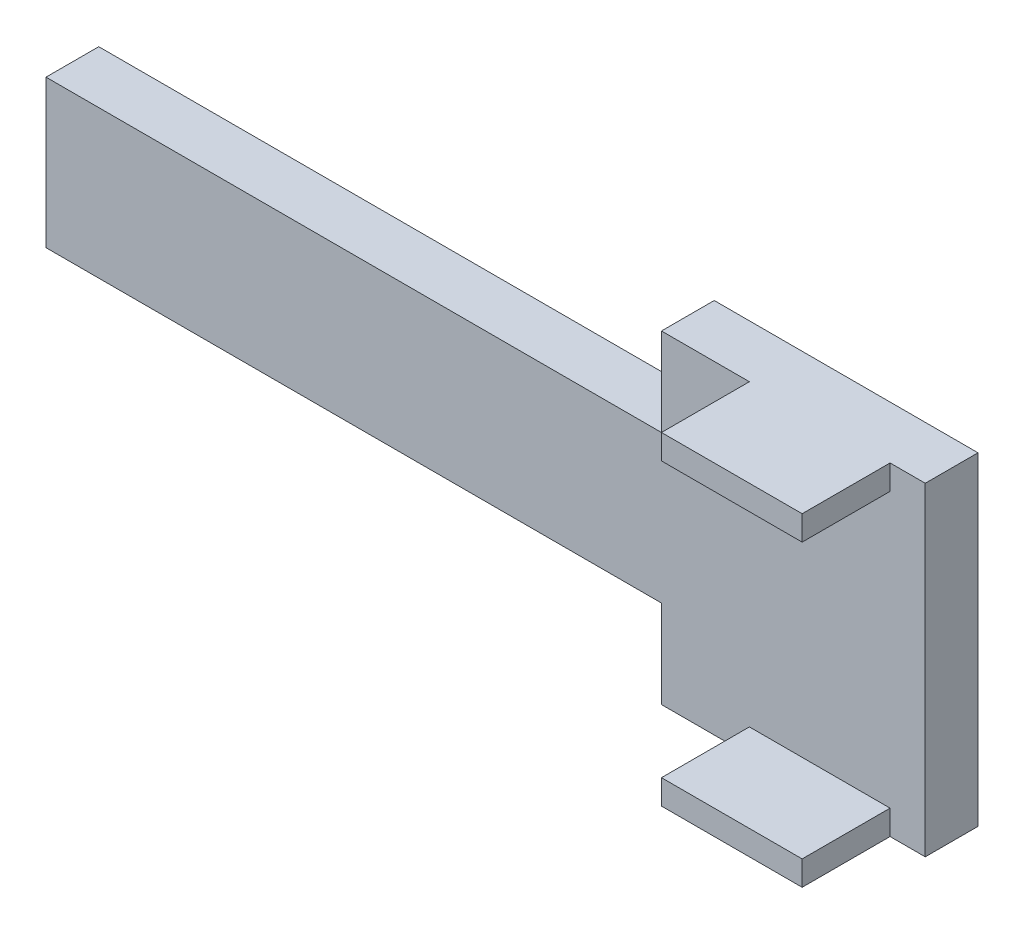
SolidWorks part; units mm, degrees
material "PPE"
ref_plane "Front Plane" through (0, 0, 0) normal (0, 0, 1) x (1, 0, 0)
ref_plane "Top Plane" through (0, 0, 0) normal (0, 1, 0) x (1, 0, 0)
ref_plane "Right Plane" through (0, 0, 0) normal (1, 0, 0) x (0, 0, -1)
sketch "Sketch2" plane through (0, 0, 0) normal (0, 0, 1) x (1, 0, 0)
  line L1 (-31.75, -11.684) -> (31.75, -11.684)
  line L2 (-31.75, -11.684) -> (-31.75, 11.684)
  line L3 (-31.75, 11.684) -> (31.75, 11.684)
  line L4 (31.75, -11.684) -> (31.75, 11.684)
  line L5 (-31.75, -11.684) -> (31.75, 11.684) construction
  line L6 (-31.75, 11.684) -> (31.75, -11.684) construction
  point P0 (0, 0)
  dimension "D1" = 63.5
  dimension "D2" = 23.368
extrude "Boss-Extrude1" add sketch "Sketch2" along normal blind 3.81
sketch "Sketch3" plane through (0, 0, 3.81) normal (0, 0, 1) x (1, 0, 0)
  line L0 (31.75, -11.684) -> (31.75, 11.684) construction
  line L3 (19.05, 9.906) -> (19.05, -9.906) construction
  line L4 (31.75, 11.684) -> (19.05, 11.684)
  line L5 (31.75, 11.684) -> (31.75, 9.906)
  line L6 (31.75, 9.906) -> (19.05, 9.906)
  line L7 (19.05, 11.684) -> (19.05, 9.906)
  line L8 (31.75, -11.684) -> (19.05, -11.684)
  line L9 (31.75, -11.684) -> (31.75, -9.906)
  line L10 (31.75, -9.906) -> (19.05, -9.906)
  line L11 (19.05, -11.684) -> (19.05, -9.906)
  dimension "D1" = 19.812
  dimension "D2" = 12.7
extrude "Boss-Extrude2" add sketch "Sketch3" along normal blind 6.35
sketch "Sketch4" plane through (0, 11.684, 0) normal (0, 1, 0) x (1, 0, 0)
  line L1 (31.75, -10.16) -> (29.21, -10.16)
  line L2 (31.75, -10.16) -> (31.75, -3.81)
  line L3 (31.75, -3.81) -> (29.21, -3.81)
  line L4 (29.21, -10.16) -> (29.21, -3.81)
  dimension "D1" = 6.35
  dimension "D2" = 2.54
extrude "Cut-Extrude1" cut sketch "Sketch4" against normal through all
sketch "Sketch5" plane through (0, 0, 3.81) normal (0, 0, 1) x (1, 0, 0)
  line L1 (-31.75, -11.684) -> (12.7, -11.684)
  line L2 (-31.75, -11.684) -> (-31.75, -5.334)
  line L3 (-31.75, -5.334) -> (12.7, -5.334)
  line L4 (12.7, -11.684) -> (12.7, -5.334)
  dimension "D1" = 44.45
  dimension "D2" = 6.35
extrude "Cut-Extrude2" cut sketch "Sketch5" against normal through all
mirror "Mirror1" about plane through (0, 0, 0) normal (0, 1, 0) of "Cut-Extrude2"
scale "Scale1" scale about centroid uniform scaling yes scale factor 1.02
